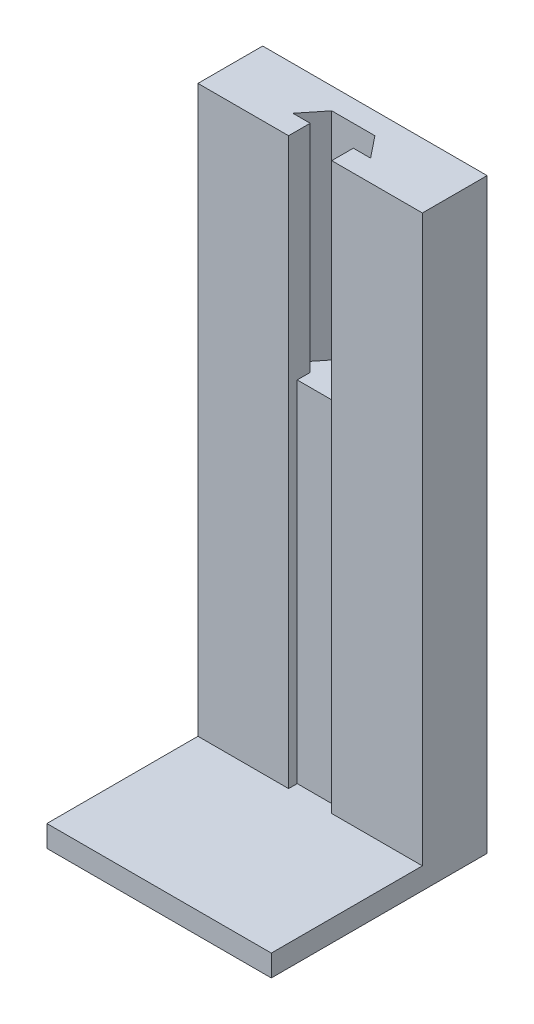
SolidWorks part; units mm, degrees
ref_plane "Front Plane" through (0, 0, 0) normal (0, 0, 1) x (1, 0, 0)
ref_plane "Top Plane" through (0, 0, 0) normal (0, 1, 0) x (1, 0, 0)
ref_plane "Right Plane" through (0, 0, 0) normal (1, 0, 0) x (0, 0, -1)
sketch "Sketch1" plane through (0, 0, 0) normal (0, 1, 0) x (1, 0, 0)
  line L1 (-26, -25) -> (26, -25)
  line L2 (-26, -25) -> (-26, 25)
  line L3 (-26, 25) -> (26, 25)
  line L4 (26, -25) -> (26, 25)
  line L5 (-26, -25) -> (26, 25) construction
  line L6 (-26, 25) -> (26, -25) construction
  point P0 (0, 0)
  dimension "D1" = 50
  dimension "D2" = 52
extrude "Boss-Extrude1" add sketch "Sketch1" along normal blind 5
sketch "Sketch2" plane through (0, 5, 0) normal (0, 1, 0) x (1, 0, 0)
  line L0 (26, -25) -> (26, 25) construction
  line L1 (-26, 25) -> (26, 25)
  line L2 (-26, 25) -> (-26, 10)
  line L3 (-26, 10) -> (26, 10)
  line L4 (26, 25) -> (26, 10)
  dimension "D1" = 15
extrude "Boss-Extrude2" add sketch "Sketch2" along normal blind 131
sketch "Sketch3" plane through (0, 136, 0) normal (0, 1, 0) x (1, 0, 0)
  line L0 (0, 25) -> (0, 10) construction
  line L1 (26, 25) -> (-26, 25) construction
  line L2 (-26, 10) -> (26, 10) construction
  line L3 (-5, 10) -> (5, 10)
  line L4 (-26, 10) -> (26, 10) construction
  line L5 (5, 10) -> (5, 15)
  line L6 (5, 15) -> (9, 15)
  line L7 (9, 15) -> (5, 20)
  line L8 (5, 20) -> (-5, 20)
  line L9 (-5, 20) -> (-9, 15)
  line L10 (-9, 15) -> (-5, 15)
  line L11 (-5, 15) -> (-5, 10)
  point P10 (0, 0)
  point P17 (0, 0)
  point P18 (0, 0)
  point P19 (0, 0)
  point P20 (0, 0)
  dimension "D1" = 10
  dimension "D2" = 5
  dimension "D3" = 5
  dimension "D4" = 4
extrude "Cut-Extrude1" cut sketch "Sketch3" against normal blind 50
sketch "Sketch4" plane through (0, 86, 0) normal (0, 1, 0) x (1, 0, 0)
  line L0 (-5, 10) -> (5, 10) construction
  line L1 (-5, 10) -> (5, 10)
  line L2 (-5, 10) -> (-5, 12)
  line L3 (-5, 12) -> (5, 12)
  line L4 (5, 10) -> (5, 12)
  line L5 (0, 20) -> (0, 10) construction
  line L6 (5, 20) -> (-5, 20) construction
  line L7 (-5, 15) -> (-5, 10) construction
  point P10 (0, 0)
  point P11 (0, 0)
  dimension "D1" = 2
extrude "Cut-Extrude2" cut sketch "Sketch4" against normal blind 81
